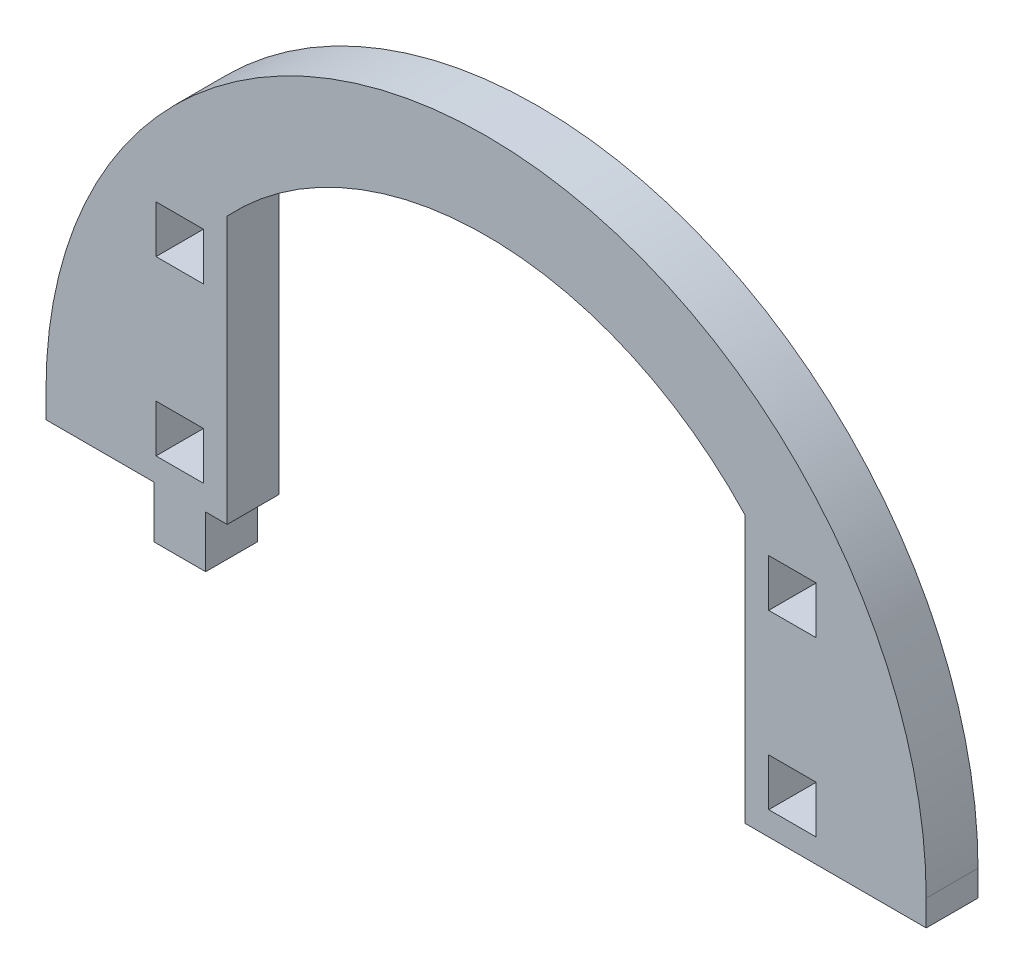
SolidWorks part; units mm, degrees
ref_plane "Front Plane" through (0, 0, 0) normal (0, 0, 1) x (1, 0, 0)
ref_plane "Top Plane" through (0, 0, 0) normal (0, 1, 0) x (1, 0, 0)
ref_plane "Right Plane" through (0, 0, 0) normal (1, 0, 0) x (0, 0, -1)
sketch "Model" plane through (0, 0, 0) normal (0, 0, 1) x (1, 0, 0)
  line L0 (3321.5255, 1259.8773) -> (3321.5255, 1256.8773)
  line L1 (3423.5255, 1259.8773) -> (3423.5255, 1256.8773)
  line L2 (3413.5255, 1256.8773) -> (3423.5255, 1256.8773)
  line L3 (3410.7755, 1265.1273) -> (3405.2755, 1265.1273)
  line L4 (3405.2755, 1265.1273) -> (3405.2755, 1259.6273)
  line L5 (3405.2755, 1259.6273) -> (3410.7755, 1259.6273)
  line L6 (3410.7755, 1259.6273) -> (3410.7755, 1265.1273)
  line L7 (3402.5255, 1256.8773) -> (3413.5255, 1256.8773)
  line L8 (3410.7755, 1285.1273) -> (3405.2755, 1285.1273)
  line L9 (3405.2755, 1285.1273) -> (3405.2755, 1279.6273)
  line L10 (3405.2755, 1279.6273) -> (3410.7755, 1279.6273)
  line L11 (3410.7755, 1279.6273) -> (3410.7755, 1285.1273)
  line L12 (3339.7755, 1265.1273) -> (3334.2755, 1265.1273)
  line L13 (3334.2755, 1265.1273) -> (3334.2755, 1259.6273)
  line L14 (3334.2755, 1259.6273) -> (3339.7755, 1259.6273)
  line L15 (3339.7755, 1259.6273) -> (3339.7755, 1265.1273)
  line L16 (3340.0255, 1256.8773) -> (3342.5255, 1256.8773)
  line L17 (3334.0255, 1256.8773) -> (3334.0255, 1250.8773)
  line L18 (3334.0255, 1250.8773) -> (3340.0255, 1250.8773)
  line L19 (3340.0255, 1250.8773) -> (3340.0255, 1256.8773)
  line L20 (3339.7755, 1285.1273) -> (3334.2755, 1285.1273)
  line L21 (3334.2755, 1285.1273) -> (3334.2755, 1279.6273)
  line L22 (3334.2755, 1279.6273) -> (3339.7755, 1279.6273)
  line L23 (3339.7755, 1279.6273) -> (3339.7755, 1285.1273)
  line L24 (3342.5255, 1287.8237) -> (3342.5255, 1256.8773)
  line L25 (3402.5255, 1287.8237) -> (3402.5255, 1256.8773)
  line L26 (3321.5255, 1256.8773) -> (3334.0255, 1256.8773)
  arc A0 (3423.5255, 1259.8773) -> (3321.5255, 1259.8773) centre (3372.5255, 1259.8773) ccw
  arc A1 (3402.5255, 1287.8237) -> (3342.5255, 1287.8237) centre (3372.5255, 1259.8773) ccw
extrude "Boss-Extrude1" add sketch "Model" along normal blind 6 contours L22 L23 L20 L21 | L14 L15 L12 L13 | L10 L11 L8 L9 | L5 L6 L3 L4 | A0 L0 L26 L17 L18 L19 L16 L24 A1 L25 L7 L2 L1
